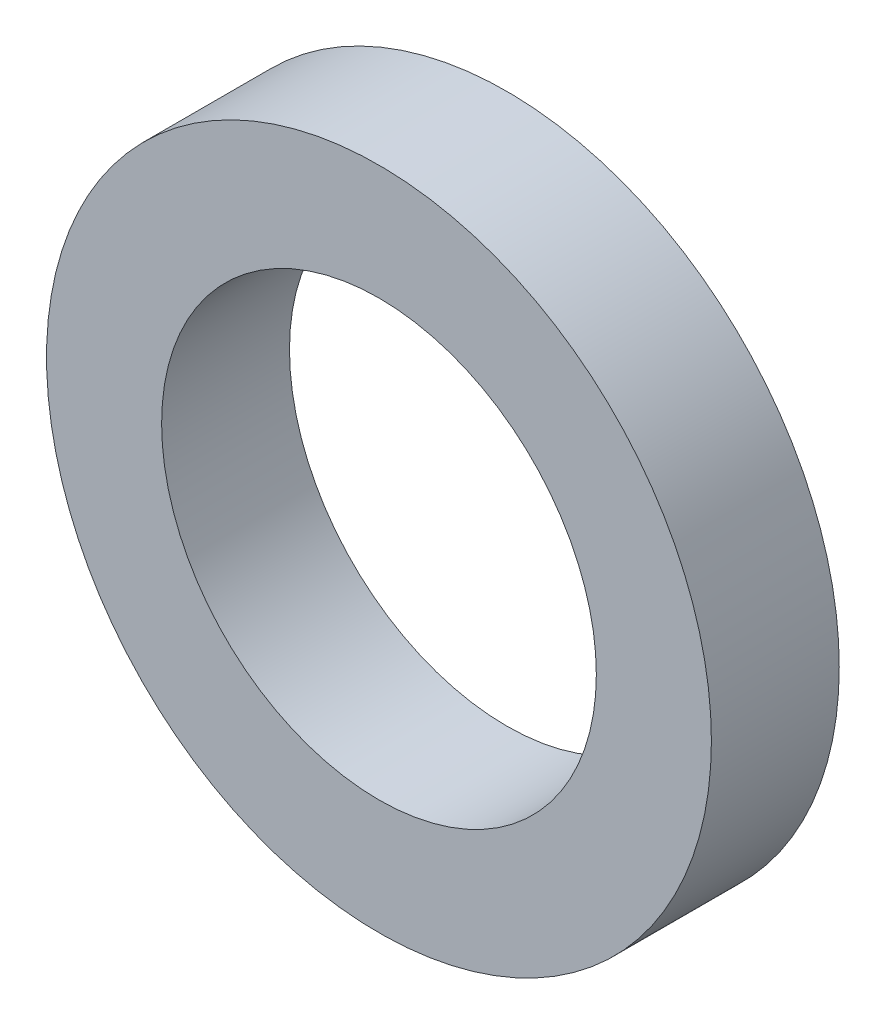
SolidWorks part; units mm, degrees
ref_plane "前视基准面" through (0, 0, 0) normal (0, 0, 1) x (1, 0, 0)
ref_plane "上视基准面" through (0, 0, 0) normal (0, 1, 0) x (1, 0, 0)
ref_plane "右视基准面" through (0, 0, 0) normal (1, 0, 0) x (0, 0, -1)
other "Configuration Table"
sketch "草图1" plane through (0, 0, 0) normal (0, 0, 1) x (1, 0, 0)
  circle A0 centre (0, 0) radius 8.5
  circle A1 centre (0, 0) radius 13
  dimension "D1" = 17
  dimension "D2" = 26
extrude "凸台-拉伸1" add sketch "草图1" along normal blind 5
